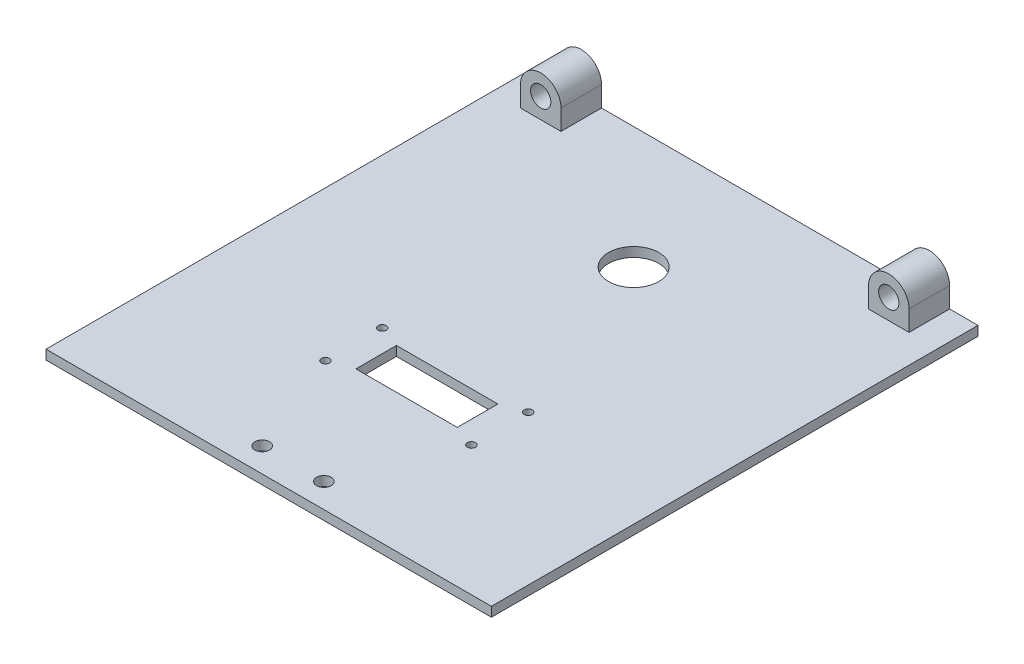
SolidWorks part; units mm, degrees
ref_plane "Front Plane" through (0, 0, 0) normal (0, 0, 1) x (1, 0, 0)
ref_plane "Top Plane" through (0, 0, 0) normal (0, 1, 0) x (1, 0, 0)
ref_plane "Right Plane" through (0, 0, 0) normal (1, 0, 0) x (0, 0, -1)
sketch "Sketch1" plane through (0, 0, 0) normal (0, 1, 0) x (1, 0, 0)
  line L1 (0, 0) -> (139.5, 0)
  line L2 (0, 0) -> (0, 152.4)
  line L3 (0, 152.4) -> (139.5, 152.4)
  line L4 (139.5, 0) -> (139.5, 152.4)
  dimension "D1" = 152.4
  dimension "D2" = 139.5
extrude "Boss-Extrude1" add sketch "Sketch1" along normal blind 6.35
sketch "Sketch2" plane through (0, 6.35, 0) normal (0, 1, 0) x (1, 0, 0)
  line L0 (0, 0) -> (139.5, 0) construction
  line L1 (0, 152.4) -> (139.5, 152.4)
  line L2 (0, 152.4) -> (0, 0)
  line L3 (0, 0) -> (139.5, 0)
  line L4 (139.5, 152.4) -> (139.5, 0)
  line L5 (139.5, 0) -> (139.5, 152.4) construction
extrude "Cut-Extrude1" cut sketch "Sketch2" against normal blind 3.375
sketch "Sketch4" plane through (0, 0, -152.4) normal (0, 0, -1) x (-1, 0, 0)
  line L0 (-130.61, 9.325) -> (-130.61, 2.975)
  line L1 (-130.61, 2.975) -> (-117.91, 2.975)
  line L2 (-117.91, 9.325) -> (-117.91, 2.975)
  line L3 (-21.59, 9.325) -> (-21.59, 2.975)
  line L4 (-21.59, 2.975) -> (-8.89, 2.975)
  line L5 (-8.89, 9.325) -> (-8.89, 2.975)
  line L6 (-139.5, 2.975) -> (0, 2.975) construction
  line L7 (0, 2.975) -> (0, 0) construction
  line L8 (-139.5, 2.975) -> (-139.5, 0) construction
  arc A0 (-117.91, 9.325) -> (-130.61, 9.325) centre (-124.26, 9.325) ccw
  circle A1 centre (-124.26, 9.325) radius 3.175
  arc A2 (-8.89, 9.325) -> (-21.59, 9.325) centre (-15.24, 9.325) ccw
  circle A3 centre (-15.24, 9.325) radius 3.175
  dimension "D1" = 6.35
  dimension "D3" = 6.35
  dimension "D5" = 6.35
  dimension "D7" = 6.35
  dimension "D2" = 6.35
  dimension "D4" = 12.7
  dimension "D6" = 6.35
  dimension "D8" = 12.7
  dimension "D9" = 8.89
  dimension "D10" = 8.89
  dimension "D11" = 15.24
  dimension "D12" = 15.24
extrude "Boss-Extrude3" add sketch "Sketch4" against normal blind 12.7
sketch "Sketch5" plane through (0, 0, 0) normal (0, -1, 0) x (1, 0, 0)
  line L0 (139.5, -152.4) -> (0, -152.4) construction
  circle A0 centre (69.75, -114.3) radius 7.874
  point P4 (69.75, -152.4)
  dimension "D1" = 15.748
  dimension "D2" = 38.1
extrude "Cut-Extrude2" cut sketch "Sketch5" against normal through all
sketch "Sketch6" plane through (0, 2.975, 0) normal (0, 1, 0) x (1, 0, 0)
  line L0 (0, 0) -> (139.5, 0) construction
  line L2 (69.75, 152.4) -> (69.75, 0) construction
  line L3 (117.91, 152.4) -> (21.59, 152.4) construction
  circle A0 centre (60.098, 7.62) radius 2.286
  circle A1 centre (79.402, 7.62) radius 2.286
  dimension "D3" = 4.572
  dimension "D4" = 7.62
  dimension "D1" = 9.652
  dimension "D2" = 9.652
  dimension "D6" = 7.62
extrude "Cut-Extrude3" cut sketch "Sketch6" against normal through all
sketch "Sketch7" plane through (0, 0, 0) normal (0, -1, 0) x (1, 0, 0)
  line L0 (44.35, -38.1) -> (44.35, -60.96) construction
  line L1 (44.35, -60.96) -> (95.15, -60.96) construction
  line L2 (95.15, -60.96) -> (95.15, -38.1) construction
  line L3 (95.15, -38.1) -> (44.35, -38.1) construction
  line L4 (0, 0) -> (139.5, 0) construction
  line L6 (53.875, -43.18) -> (85.625, -43.18)
  line L7 (53.875, -43.18) -> (53.875, -55.88)
  line L8 (53.875, -55.88) -> (85.625, -55.88)
  line L9 (85.625, -43.18) -> (85.625, -55.88)
  circle A0 centre (46.89, -40.64) radius 1.27
  circle A1 centre (92.61, -40.64) radius 1.27
  circle A2 centre (92.61, -58.42) radius 1.27
  circle A3 centre (46.89, -58.42) radius 1.27
  point P2 (69.75, -38.1)
  point P7 (69.75, 0)
  point P17 (85.625, -49.53)
  point P21 (95.15, -49.53)
  point P22 (69.75, -55.88)
  point P23 (69.75, -60.96)
  dimension "D4" = 2.54
  dimension "D1" = 50.8
  dimension "D2" = 22.86
  dimension "D3" = 38.1
  dimension "D5" = 2.54
  dimension "D6" = 2.54
  dimension "D7" = 17.78
  dimension "D8" = 2.54
  dimension "D9" = 12.7
  dimension "D10" = 31.75
extrude "Cut-Extrude4" cut sketch "Sketch7" against normal through all and the other way through all
